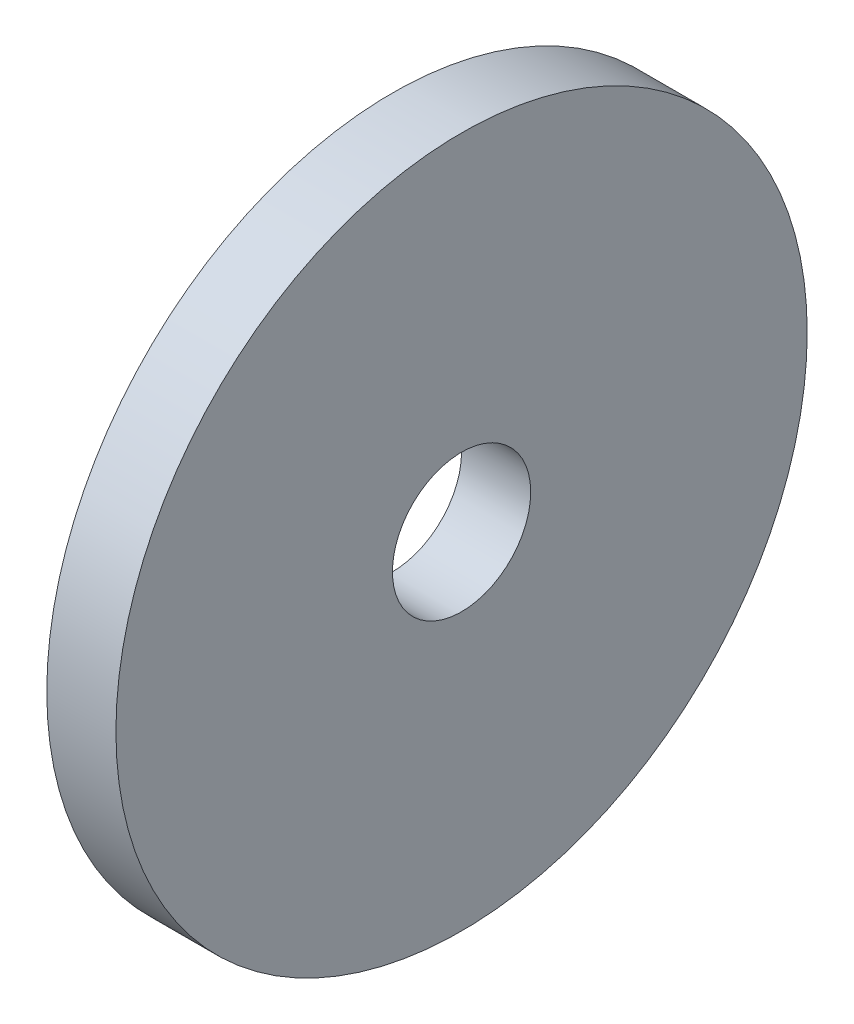
SolidWorks part; units mm, degrees
material "Pine"
ref_plane "Front Plane" through (0, 0, 0) normal (0, 0, 1) x (1, 0, 0)
ref_plane "Top Plane" through (0, 0, 0) normal (0, 1, 0) x (1, 0, 0)
ref_plane "Right Plane" through (0, 0, 0) normal (1, 0, 0) x (0, 0, -1)
sketch "Sketch1" plane through (0, 0, 0) normal (1, 0, 0) x (0, 0, -1)
  circle A0 centre (0, 0) radius 10
  dimension "D1" = 20
extrude "Boss-Extrude1" add sketch "Sketch1" along normal blind 2
sketch "Sketch2" plane through (2, 0, 0) normal (1, 0, 0) x (0, 0, -1)
  circle A2 centre (0, 0) radius 2
  dimension "D1" = 4
extrude "Cut-Extrude1" cut sketch "Sketch2" against normal through all
